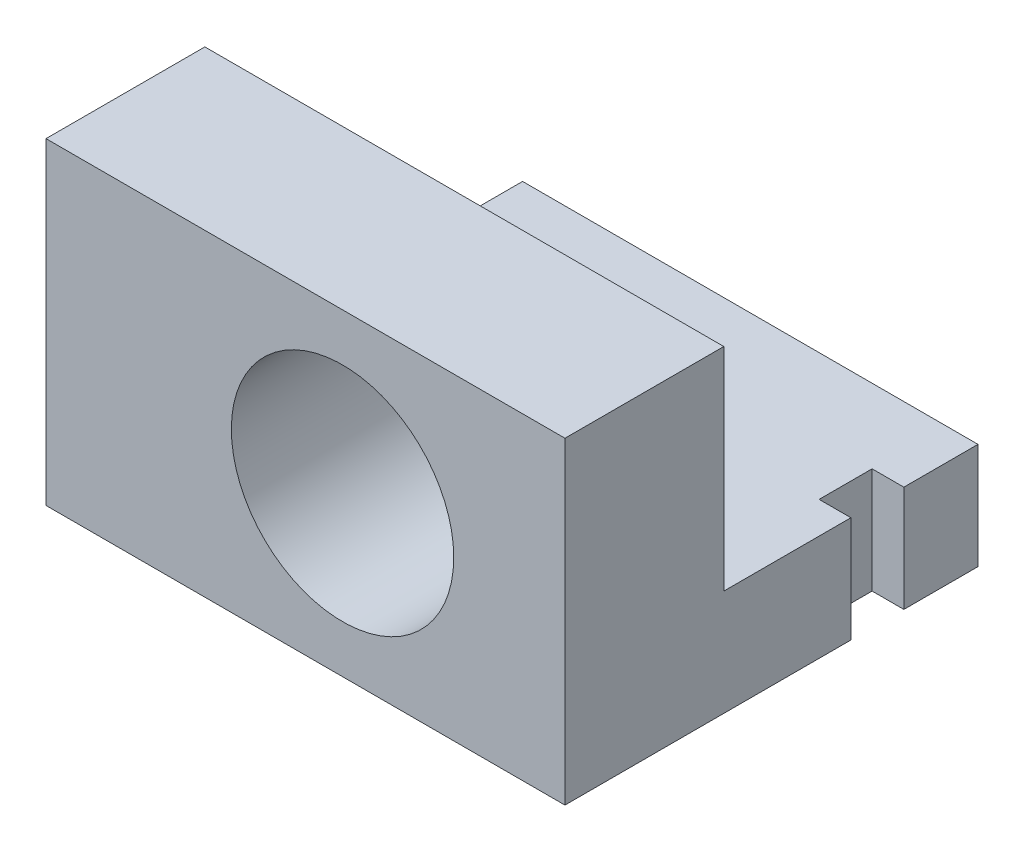
SolidWorks part; units mm, degrees
ref_plane "Front Plane" through (0, 0, 0) normal (0, 0, 1) x (1, 0, 0)
ref_plane "Top Plane" through (0, 0, 0) normal (0, 1, 0) x (1, 0, 0)
ref_plane "Right Plane" through (0, 0, 0) normal (1, 0, 0) x (0, 0, -1)
sketch "Sketch1" plane through (0, 0, 0) normal (0, 0, 1) x (1, 0, 0)
  line L1 (-24.5, 15) -> (24.5, 15)
  line L2 (-24.5, 15) -> (-24.5, -15)
  line L3 (-24.5, -15) -> (24.5, -15)
  line L4 (24.5, 15) -> (24.5, -15)
  dimension "D1" = 49
  dimension "D2" = 30
  dimension "D3" = 15
  dimension "D4" = 24.5
extrude "Boss-Extrude1" add sketch "Sketch1" along normal blind 15
sketch "Sketch3" plane through (0, 0, 0) normal (0, 0, -1) x (-1, 0, 0)
  line L0 (-24.5, -15) -> (-24.5, 15) construction
  circle A0 centre (-3.5, 0) radius 10.5
  point P2 (0, 0)
  point P5 (0, 0)
  dimension "D1" = 21
  dimension "D2" = 21
extrude "Cut-Extrude1" cut sketch "Sketch3" against normal blind 23
sketch "Sketch4" plane through (0, 0, 0) normal (0, 0, -1) x (-1, 0, 0)
  line L1 (-24.5, -15) -> (18.5, -15)
  line L2 (-24.5, -15) -> (-24.5, -5)
  line L3 (-24.5, -5) -> (18.5, -5)
  line L4 (18.5, -15) -> (18.5, -5)
  dimension "D1" = 43
  dimension "D2" = 10
extrude "Boss-Extrude3" add sketch "Sketch4" along normal blind 24
sketch "Sketch5" plane through (-18.5, 0, 0) normal (-1, 0, 0) x (0, 0, 1)
  line L0 (-24, -15) -> (-24, -5) construction
  line L1 (-17, -5) -> (-12, -5)
  line L2 (-17, -5) -> (-17, -15)
  line L3 (-17, -15) -> (-12, -15)
  line L4 (-12, -5) -> (-12, -15)
  line L5 (-24, -5) -> (0, -5) construction
  line L6 (-24, -15) -> (0, -15) construction
  dimension "D1" = 7
  dimension "D2" = 5
extrude "Cut-Extrude2" cut sketch "Sketch5" against normal blind 3
ref_plane "Plane1" through (3, 0, 0) normal (-1, 0, 0) x (0, 0, 1)
mirror "Mirror1" about plane through (3, 0, 0) normal (-1, 0, 0) of "Cut-Extrude2"
